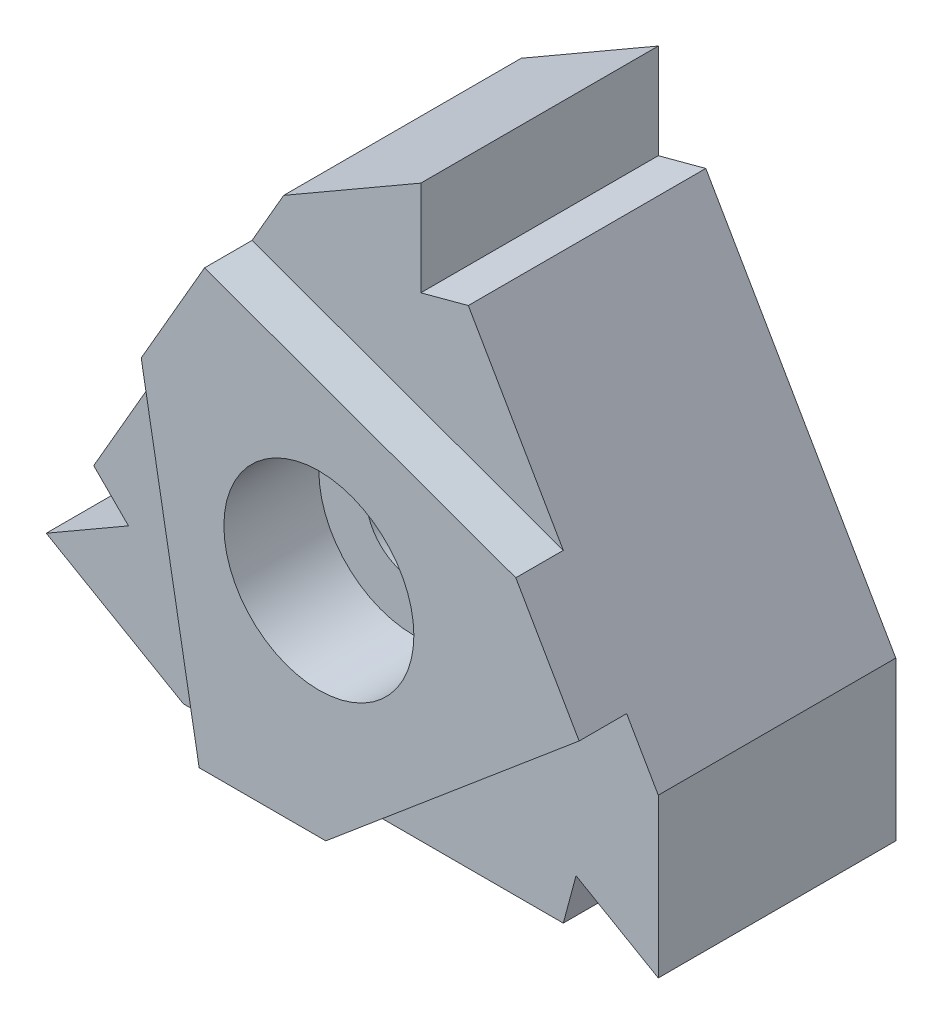
SolidWorks part; units mm, degrees
ref_plane "前视基准面" through (0, 0, 0) normal (0, 0, 1) x (1, 0, 0)
ref_plane "上视基准面" through (0, 0, 0) normal (0, 1, 0) x (1, 0, 0)
ref_plane "右视基准面" through (0, 0, 0) normal (1, 0, 0) x (0, 0, -1)
sketch "草图1" plane through (0, 0, 0) normal (0, 0, 1) x (1, 0, 0)
  line L0 (-40.4046, 0) -> (-28.4046, 0) construction
  line L2 (-37.2348, 15.4904) -> (-43.2348, 5.0981)
  line L3 (-40.4046, 0) -> (-28.4046, 0)
  line L4 (-25.4046, 5) -> (-31.4046, 15.3923)
  line L5 (-40.4046, 0) -> (-44.7348, 2.5)
  line L6 (-44.7348, 2.5) -> (-42.1367, 4)
  line L7 (-42.1367, 4) -> (-43.2348, 5.0981)
  line L8 (-37.2348, 15.4904) -> (-32.9046, 17.9904)
  line L9 (-32.9046, 17.9904) -> (-32.9046, 14.9904)
  line L10 (-25.4046, 5) -> (-25.4046, 0)
  line L11 (-24.1781, 0) -> (83.4636, 0) construction
  line L22 (-32.9046, 14.9904) -> (-31.4046, 15.3923)
  line L24 (-25.4046, 0) -> (-28.0027, 1.5)
  line L25 (-28.0027, 1.5) -> (-28.4046, 0)
  dimension "D1" = 60
  dimension "D2" = 60
  dimension "D3" = 150
  dimension "D4" = 5
  dimension "D5" = 12
  dimension "D6" = 60
  dimension "D7" = 75
  dimension "D8" = 3
  dimension "D9" = 150
  dimension "D10" = 75
  dimension "D11" = 3
  dimension "D12" = 5
  dimension "D13" = 150
  dimension "D14" = 5
  dimension "D15" = 60
  dimension "D16" = 3
  dimension "D17" = 75
extrude "凸台-拉伸1" add sketch "草图1" along normal blind 9
sketch "草图2" plane through (0, 0, 9) normal (0, 0, 1) x (1, 0, 0)
  line L0 (-38.4046, 0) -> (-40.2348, 10.2942)
  line L3 (-40.4046, 0) -> (-28.4046, 0) construction
  line L5 (-37.2348, 15.4904) -> (-43.2348, 5.0981) construction
  line L6 (-38.2348, 13.7583) -> (-28.4046, 10.1962)
  line L7 (-25.4046, 5) -> (-31.4046, 15.3923) construction
  line L8 (-26.4046, 6.7321) -> (-34.4046, 0)
  line L9 (-40.2348, 10.2942) -> (-43.2348, 5.0981)
  line L10 (-43.2348, 5.0981) -> (-42.1367, 4)
  line L11 (-42.1367, 4) -> (-44.7348, 2.5)
  line L12 (-44.7348, 2.5) -> (-40.4046, 0)
  line L13 (-40.4046, 0) -> (-38.4046, 0)
  line L14 (-34.4046, 0) -> (-28.4046, 0)
  line L15 (-28.4046, 0) -> (-28.0027, 1.5)
  line L16 (-28.0027, 1.5) -> (-25.4046, 0)
  line L17 (-25.4046, 0) -> (-25.4046, 5)
  line L18 (-25.4046, 5) -> (-26.4046, 6.7321)
  line L19 (-28.4046, 10.1962) -> (-31.4046, 15.3923)
  line L20 (-31.4046, 15.3923) -> (-32.9046, 14.9904)
  line L21 (-32.9046, 14.9904) -> (-32.9046, 17.9904)
  line L22 (-32.9046, 17.9904) -> (-37.2348, 15.4904)
  line L23 (-37.2348, 15.4904) -> (-38.2348, 13.7583)
  dimension "D1" = 2
  dimension "D2" = 2
  dimension "D3" = 2
extrude "切除-拉伸5" cut sketch "草图2" against normal blind 1.5
hole_wizard "孔1" positions "草图5" profile "草图6" legacy end condition through all
sketch "草图5" plane through (0, 0, 9) normal (0, 0, 1) x (1, 0, 0)
  line L0 (-38.2348, 13.7583) -> (-40.2348, 10.2942) construction
  point P0 (-34.6241, 7.0121)
  dimension "D1" = 6.5
sketch "草图6" plane through (-34.6241, 7.0121, 9) normal (1, 0, 0) x (0, -1, 0)
  line L0 (0, 0) -> (0, 9)
  line L1 (0, 9) -> (1.5, 9)
  line L3 (1.5, 9) -> (1.5, 3)
  line L4 (1.5, 3) -> (3, 3)
  line L5 (3, 3) -> (3, 0)
  line L7 (3, 0) -> (0, 0)
  line L11 (0, -6.35) -> (0, 107.95) construction
  dimension "通孔孔直径" = 3
  dimension "通孔孔深度" = 9
  dimension "柱形沉头孔直径" = 6
  dimension "柱形沉头孔深度" = 3
cosmetic thread "装饰螺纹线1" parameters "D1"=9, "D2"=9
